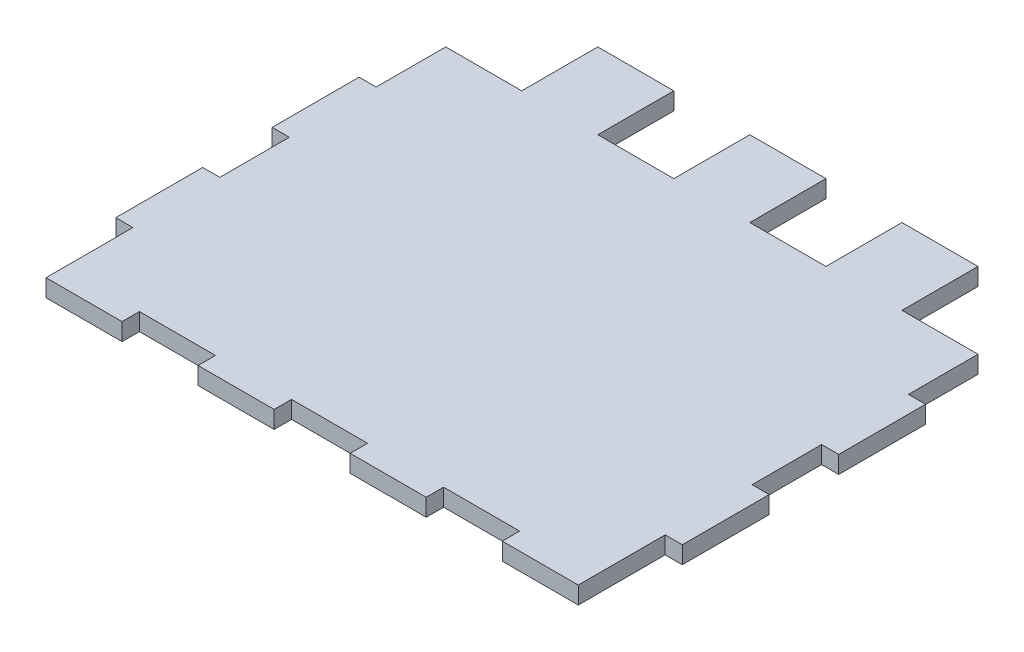
SolidWorks part; units mm, degrees
ref_plane "Front Plane" through (0, 0, 0) normal (0, 0, 1) x (1, 0, 0)
ref_plane "Top Plane" through (0, 0, 0) normal (0, 1, 0) x (1, 0, 0)
ref_plane "Right Plane" through (0, 0, 0) normal (1, 0, 0) x (0, 0, -1)
sketch "Sketch3" plane through (0, 0, 0) normal (0, 1, 0) x (1, 0, 0)
  line L0 (-283.144, 20.32) -> (-260.9155, 20.32)
  line L1 (-260.9155, 20.32) -> (-260.9155, 42.5486)
  line L2 (-260.9155, 42.5486) -> (-238.6869, 42.5486)
  line L3 (-238.6869, 42.5486) -> (-238.6869, 20.32)
  line L4 (-238.6869, 20.32) -> (-216.4583, 20.32)
  line L5 (-216.4583, 20.32) -> (-216.4583, 42.5486)
  line L6 (-216.4583, 42.5486) -> (-194.2297, 42.5486)
  line L7 (-194.2297, 42.5486) -> (-194.2297, 20.32)
  line L8 (-194.2297, 20.32) -> (-172.0012, 20.32)
  line L9 (-172.0012, 20.32) -> (-172.0012, 42.5486)
  line L10 (-172.0012, 42.5486) -> (-149.7726, 42.5486)
  line L11 (-149.7726, 42.5486) -> (-149.7726, 20.32)
  line L12 (-149.7726, 20.32) -> (-127.544, 20.32)
  line L13 (-127.544, 20.32) -> (-127.544, 0)
  line L14 (-127.544, 0) -> (-122.544, 0)
  line L15 (-122.544, 0) -> (-122.544, -25.4)
  line L16 (-122.544, -25.4) -> (-127.544, -25.4)
  line L17 (-127.544, -25.4) -> (-127.544, -45.72)
  line L18 (-127.544, -45.72) -> (-122.544, -45.72)
  line L19 (-122.544, -45.72) -> (-122.544, -71.12)
  line L20 (-122.544, -71.12) -> (-127.544, -71.12)
  line L21 (-127.544, -71.12) -> (-127.544, -96.52)
  line L22 (-127.544, -96.52) -> (-149.7726, -96.52)
  line L26 (-172.0012, -96.52) -> (-194.2297, -96.52)
  line L30 (-216.4583, -96.52) -> (-238.6869, -96.52)
  line L34 (-260.9155, -96.52) -> (-283.144, -96.52)
  line L35 (-283.144, -96.52) -> (-283.144, -71.12)
  line L36 (-283.144, -71.12) -> (-288.144, -71.12)
  line L37 (-288.144, -71.12) -> (-288.144, -45.72)
  line L38 (-288.144, -45.72) -> (-283.144, -45.72)
  line L39 (-283.144, -45.72) -> (-283.144, -25.4)
  line L40 (-283.144, -25.4) -> (-288.144, -25.4)
  line L41 (-288.144, -25.4) -> (-288.144, 0)
  line L42 (-288.144, 0) -> (-283.144, 0)
  line L43 (-283.144, 0) -> (-283.144, 20.32)
  line L44 (-260.9155, -96.52) -> (-260.9155, -91.44)
  line L46 (-260.9155, -91.44) -> (-238.6869, -91.44)
  line L48 (-238.6869, -91.44) -> (-238.6869, -96.52)
  line L49 (-216.4583, -96.52) -> (-216.4583, -91.44)
  line L50 (-216.4583, -91.44) -> (-194.2297, -91.44)
  line L51 (-194.2297, -91.44) -> (-194.2297, -96.52)
  line L52 (-172.0012, -96.52) -> (-172.0012, -91.44)
  line L53 (-172.0012, -91.44) -> (-149.7726, -91.44)
  line L54 (-149.7726, -91.44) -> (-149.7726, -96.52)
  dimension "D1" = 22.2286
  dimension "D2" = 22.2286
  dimension "D3" = 22.2286
  dimension "D4" = 22.2286
  dimension "D5" = 22.2286
  dimension "D6" = 22.2286
  dimension "D7" = 22.2286
  dimension "D8" = 22.2286
  dimension "D9" = 22.2286
  dimension "D10" = 22.2286
  dimension "D11" = 22.2286
  dimension "D12" = 22.2286
  dimension "D13" = 22.2286
  dimension "D14" = 22.2286
  dimension "D15" = 5.08
  dimension "D16" = 22.2286
  dimension "D17" = 22.2286
  dimension "D18" = 22.2286
  dimension "D19" = 22.2286
  dimension "D20" = 22.2286
  dimension "D21" = 22.2286
  dimension "D22" = 5.08
  dimension "D23" = 5.08
  dimension "D24" = 5.08
  dimension "D25" = 5.08
  dimension "D27" = 20.32
  dimension "D28" = 25.4
  dimension "D29" = 20.32
  dimension "D30" = 25.4
  dimension "D31" = 20.32
  dimension "D32" = 25.4
  dimension "D33" = 20.32
  dimension "D34" = 25.4
  dimension "D35" = 25.4
  dimension "D36" = 25.4
  dimension "D37" = 5
  dimension "D38" = 5
  dimension "D39" = 5
  dimension "D40" = 5
  dimension "D41" = 5
  dimension "D42" = 5
  dimension "D43" = 5
extrude "Boss-Extrude2" add sketch "Sketch3" along normal blind 5.08
